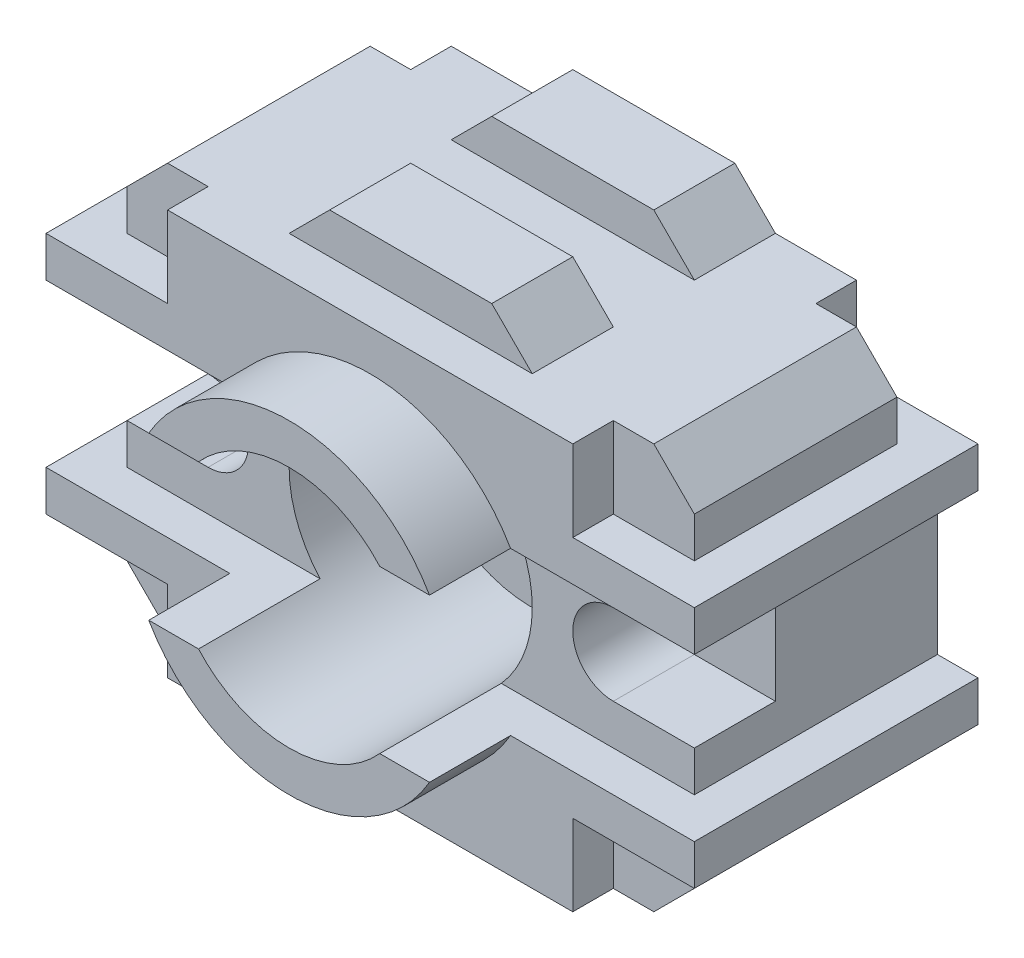
SolidWorks part; units mm, degrees
ref_plane "Front Plane" through (0, 0, 0) normal (0, 0, 1) x (1, 0, 0)
ref_plane "Top Plane" through (0, 0, 0) normal (0, 1, 0) x (1, 0, 0)
ref_plane "Right Plane" through (0, 0, 0) normal (1, 0, 0) x (0, 0, -1)
sketch "Sketch2" plane through (0, 0, 0) normal (0, 0, 1) x (1, 0, 0)
  line L0 (-70, 40) -> (-65, 45)
  line L1 (-65, 45) -> (-5, 45)
  line L2 (-5, 45) -> (0, 40)
  line L3 (0, 40) -> (0, 0)
  line L4 (0, 0) -> (-5, -5)
  line L5 (-5, -5) -> (-65, -5)
  line L6 (-65, -5) -> (-70, 0)
  line L7 (-70, 0) -> (-70, 40)
  dimension "D1" = 5
  dimension "5" = 5
  dimension "D2" = 5
  dimension "D3" = 5
  dimension "D4" = 5
  dimension "D5" = 5
  dimension "40" = 40
  dimension "D7" = 60
extrude "Boss-Extrude2" add sketch "Sketch2" along normal blind 30
sketch "Sketch4" plane through (0, 0, 30) normal (0, 0, 1) x (1, 0, 0)
  line L0 (-50, 45) -> (-45, 50)
  line L1 (-5, 45) -> (-65, 45) construction
  line L2 (-45, 50) -> (-25, 50)
  line L3 (-25, 50) -> (-20, 45)
  line L4 (-20, 45) -> (-50, 45)
  dimension "D1" = 15
  dimension "D2" = 5
  dimension "5" = 5
  dimension "D3" = 5
  dimension "D4" = 30
extrude "Boss-Extrude3" add sketch "Sketch4" against normal blind 10
sketch "Sketch5" plane through (0, 0, 0) normal (0, 0, -1) x (-1, 0, 0)
  line L0 (20, 45) -> (25, 50)
  line L1 (25, 50) -> (45, 50)
  line L2 (45, 50) -> (50, 45)
  line L3 (50, 45) -> (20, 45)
extrude "Boss-Extrude4" add sketch "Sketch5" against normal blind 10
sketch "Sketch6" plane through (0, 0, 30) normal (0, 0, 1) x (1, 0, 0)
  line L0 (-75, 30) -> (5, 30)
  line L1 (5, 30) -> (5, 35)
  line L2 (5, 35) -> (-10, 35)
  line L3 (-10, 35) -> (-10, 45)
  line L4 (-5, 45) -> (-20, 45) construction
  line L5 (-10, 45) -> (-60, 45)
  line L6 (-50, 45) -> (-65, 45) construction
  line L7 (-60, 45) -> (-60, 35)
  line L8 (-60, 35) -> (-75, 35)
  line L9 (-75, 35) -> (-75, 30)
  line L10 (0, 0) -> (0, 40) construction
  line L12 (-75, 10) -> (5, 10)
  line L13 (5, 10) -> (5, 5)
  line L14 (5, 5) -> (-10, 5)
  line L15 (-10, 5) -> (-10, -5)
  line L16 (-10, -5) -> (-60, -5)
  line L17 (-60, -5) -> (-60, 5)
  line L18 (-60, 5) -> (-75, 5)
  line L19 (-75, 5) -> (-75, 10)
  line L21 (-65, -5) -> (-5, -5) construction
  dimension "D1" = 5
  dimension "D2" = 15
  dimension "D3" = 5
  dimension "D4" = 10
  dimension "D5" = 15
  dimension "D6" = 50
  dimension "D7" = 5
  dimension "D8" = 80
  dimension "D9" = 50
  dimension "D10" = 10
  dimension "D11" = 15
  dimension "D12" = 5
  dimension "D13" = 5
  dimension "D14" = 5
extrude "Boss-Extrude7" add sketch "Sketch6" along normal blind 5
sketch "Sketch12" plane through (0, 0, 30) normal (0, 0, 1) x (1, 0, 0)
  line L0 (-70, 25) -> (-60, 25)
  line L1 (-70, 30) -> (-70, 10) construction
  line L2 (-60, 15) -> (-70, 15)
  line L3 (-70, 15) -> (-70, 25)
  line L4 (0, 15) -> (-10, 15)
  line L5 (0, 10) -> (0, 30) construction
  line L6 (-10, 25) -> (0, 25)
  line L7 (0, 25) -> (0, 15)
  line L8 (-75, 30) -> (5, 30) construction
  line L9 (0, 10) -> (-70, 10) construction
  arc A0 (-60, 25) -> (-60, 15) centre (-60, 20) cw
  arc A1 (-10, 15) -> (-10, 25) centre (-10, 20) cw
  dimension "D1" = 5
  dimension "D3" = 10
  dimension "D2" = 5
  dimension "D4" = 10
extrude "Cut-Extrude9" cut sketch "Sketch12" against normal blind 10
sketch "Sketch13" plane through (0, 0, 20) normal (0, 0, 1) x (1, 0, 0)
  circle A0 centre (-60, 20) radius 2.5
  circle A1 centre (-10, 20) radius 2.5
  dimension "D1" = 5
  dimension "D2" = 5
extrude "Cut-Extrude10" cut sketch "Sketch13" against normal blind 190
sketch "Sketch14" plane through (0, 0, 30) normal (0, 0, 1) x (1, 0, 0)
  line L0 (-75, 30) -> (5, 30) construction
  circle A0 centre (-35, 20) radius 15
  point P2 (-10, 20)
  point P3 (-60, 20)
  dimension "D1" = 30
  dimension "D2" = 25
  dimension "D3" = 10
extrude "Cut-Extrude12" cut sketch "Sketch14" against normal blind 15
sketch "Sketch15" plane through (0, 0, 35) normal (0, 0, 1) x (1, 0, 0)
  line L0 (-75, 30) -> (5, 30) construction
  line L1 (5, 10) -> (-75, 10) construction
  line L2 (0, 10) -> (-23.8197, 10) construction
  line L3 (-46.1803, 10) -> (-23.8197, 10)
  line L4 (-46.1803, 30) -> (-23.8197, 30)
  circle A0 centre (-35, 20) radius 15 construction
  arc A1 (-46.1803, 30) -> (-46.1803, 10) centre (-35, 20) ccw construction
  arc A2 (-23.8197, 10) -> (-23.8197, 30) centre (-35, 20) ccw construction
  arc A3 (-46.1803, 30) -> (-23.8197, 30) centre (-35, 20) cw
  arc A4 (-46.1803, 10) -> (-23.8197, 10) centre (-35, 20) ccw
  point P0 (-46.1803, 30)
  point P1 (-23.8197, 30)
  point P4 (-35, 20)
  point P5 (-46.1803, 10)
  point P7 (-23.8197, 10)
extrude "Cut-Extrude13" cut sketch "Sketch15" against normal blind 5
sketch "Sketch16" plane through (0, 0, 35) normal (0, 0, 1) x (1, 0, 0)
  line L4 (-46.1803, 30) -> (-52.3205, 30)
  line L5 (-75, 30) -> (-46.1803, 30) construction
  line L6 (-17.6795, 30) -> (-23.8197, 30)
  line L7 (-23.8197, 10) -> (-17.6795, 10)
  line L8 (5, 10) -> (-23.8197, 10) construction
  line L9 (-46.1803, 10) -> (-75, 10) construction
  line L10 (-52.3205, 10) -> (-46.1803, 10)
  arc A0 (-52.3205, 30) -> (-17.6795, 30) centre (-35, 20) cw
  arc A1 (-23.8197, 10) -> (-46.1803, 10) centre (-35, 20) cw
  arc A2 (-17.6795, 10) -> (-52.3205, 10) centre (-35, 20) cw
  arc A3 (-23.8197, 10) -> (-23.8197, 30) centre (-35, 20) ccw construction
  point P24 (-20, 20)
  point P27 (-35, 20)
  arc M1 (-46.1803, 30) -> (-23.8197, 30) centre (-35, 20) cw
  line M2 (-23.8197, 30) -> (5, 30)
  line M10 (-75, 30) -> (-46.1803, 30)
  dimension "D1" = 15
  dimension "D3" = 20
  dimension "D2" = 20
extrude "Boss-Extrude8" add sketch "Sketch16" along normal blind 10 contours A2 L7 A1 L10 | A0 M10 M1 M2
sketch "Sketch17" plane through (0, 0, 15) normal (0, 0, 1) x (1, 0, 0)
  circle A0 centre (-35, 20) radius 5
  point P0 (-35, 20)
  point P1 (-59.3592, 20)
  dimension "D1" = 10
extrude "Cut-Extrude15" cut sketch "Sketch17" against normal blind 15
ref_plane "Plane1" through (0, 0, 15) normal (0, 0, 1) x (1, 0, 0)
sketch "Sketch18" plane through (0, 0, 0) normal (0, 0, -1) x (-1, 0, 0)
  line L0 (70, 40) -> (70, 0) construction
  line L1 (60, 35) -> (71.1503, 35)
  line L2 (60, 35) -> (60, 47.4054)
  line L3 (60, 47.4054) -> (71.1503, 47.4054)
  line L4 (71.1503, 35) -> (71.1503, 47.4054)
  line L5 (50, 45) -> (65, 45) construction
  line L6 (35, 20) -> (35, 33.3304)
  line L7 (35, 33.3304) -> (35, 20)
  line L8 (35, 20) -> (48.4352, 20)
  line L9 (-1.1503, 35) -> (-1.1503, 47.4054)
  line L10 (10, 47.4054) -> (-1.1503, 47.4054)
  line L11 (10, 35) -> (10, 47.4054)
  line L12 (10, 35) -> (-1.1503, 35)
  line L13 (10, 5) -> (-1.1503, 5)
  line L14 (10, 5) -> (10, -7.4054)
  line L15 (10, -7.4054) -> (-1.1503, -7.4054)
  line L16 (-1.1503, 5) -> (-1.1503, -7.4054)
  line L17 (71.1503, 5) -> (71.1503, -7.4054)
  line L18 (60, -7.4054) -> (71.1503, -7.4054)
  line L19 (60, 5) -> (60, -7.4054)
  line L20 (60, 5) -> (71.1503, 5)
  line M8 (70, 0) -> (70, 40)
  line M9 (70, 40) -> (65, 45)
  line M10 (65, 45) -> (50, 45)
  line M14 (20, 45) -> (5, 45)
  line M15 (5, 45) -> (0, 40)
  line M16 (0, 40) -> (0, 0)
  line M17 (0, 0) -> (5, -5)
  line M18 (5, -5) -> (65, -5)
  line M19 (65, -5) -> (70, 0)
  dimension "D1" = 10
  dimension "D2" = 10
extrude "Cut-Extrude16" cut sketch "Sketch18" against normal blind 5 contours L14 L13 M16 M17 M18 | L12 L11 M14 M15 M16 | L2 L1 M8 M9 M10 | L20 L19 M18 M19 M8
sketch "Sketch19" plane through (-70, 0, 0) normal (-1, 0, 0) x (0, 0, 1)
  line L0 (0, 35) -> (0, 5) construction
  line L1 (0, 30) -> (30, 30)
  line L2 (0, 30) -> (0, 35)
  line L3 (0, 35) -> (30, 35)
  line L4 (30, 30) -> (30, 35)
  line L10 (0, 5) -> (30, 5)
  line L11 (0, 5) -> (0, 10)
  line L12 (0, 10) -> (30, 10)
  line L13 (30, 5) -> (30, 10)
  dimension "D1" = 5
extrude "Boss-Extrude9" add sketch "Sketch19" along normal blind 5
sketch "Sketch20" plane through (0, 0, 0) normal (1, 0, 0) x (0, 0, -1)
  line L1 (0, 35) -> (-30, 35)
  line L2 (0, 35) -> (0, 30)
  line L3 (0, 30) -> (-30, 30)
  line L4 (-30, 35) -> (-30, 30)
  line L5 (0, 5) -> (-30, 5)
  line L6 (0, 5) -> (0, 10)
  line L7 (0, 10) -> (-30, 10)
  line L8 (-30, 5) -> (-30, 10)
extrude "Boss-Extrude10" add sketch "Sketch20" along normal blind 5
